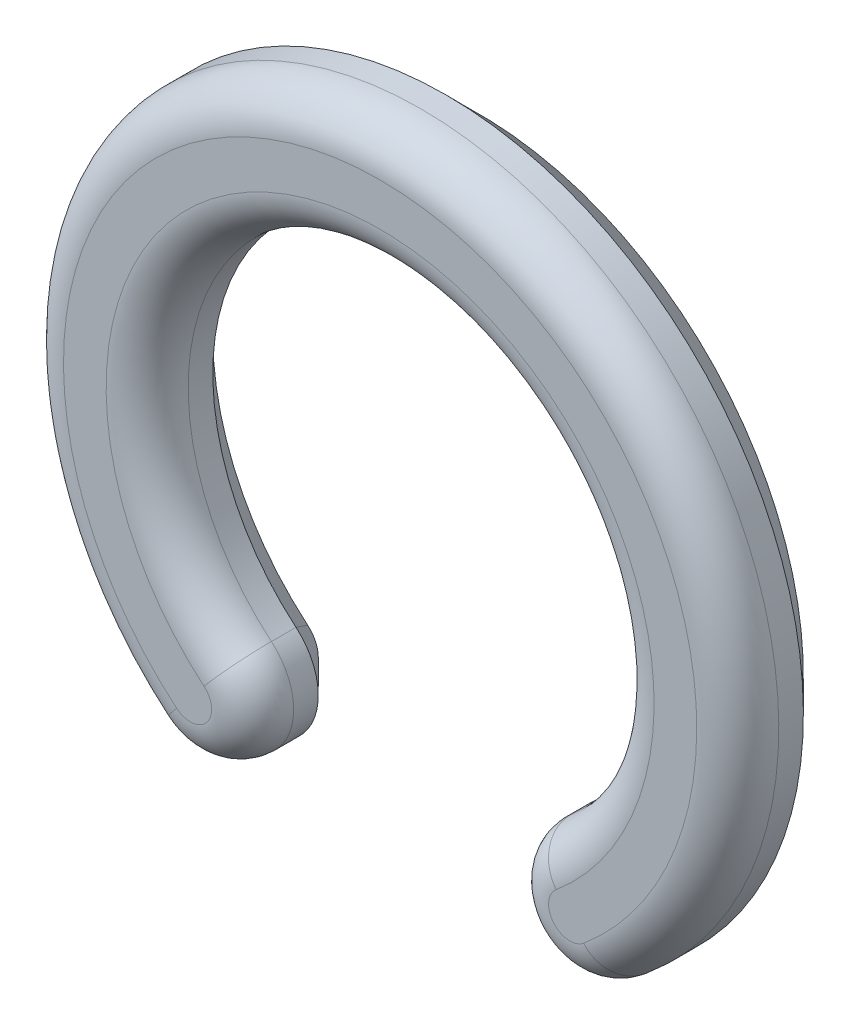
SolidWorks part; units mm, degrees
material "ABS"
ref_plane "Front Plane" through (0, 0, 0) normal (0, 0, 1) x (1, 0, 0)
ref_plane "Top Plane" through (0, 0, 0) normal (0, 1, 0) x (1, 0, 0)
ref_plane "Right Plane" through (0, 0, 0) normal (1, 0, 0) x (0, 0, -1)
sketch "Sketch1" plane through (0, 0, 0) normal (0, 0, 1) x (1, 0, 0)
  arc A0 (4.5638, -5.4389) -> (-4.5638, -5.4389) centre (0, 0) ccw
  arc A1 (7.0064, -8.3499) -> (-7.0064, -8.3499) centre (0, 0) ccw
  arc A2 (-7.0064, -8.3499) -> (-4.5638, -5.4389) centre (-5.7851, -6.8944) ccw
  arc A3 (4.5638, -5.4389) -> (7.0064, -8.3499) centre (5.7851, -6.8944) ccw
  point P1 (0, 0)
  dimension "D1" = 3.8
  dimension "D2" = 80
  dimension "D3" = 7.1
extrude "Boss-Extrude1" add sketch "Sketch1" along normal blind 3
chamfer "Chamfer1" distance 1 angle 45 4 edges at (0, 7.1, 0) (4.3296, -8.1157, 0) (-4.3296, -8.1157, 0) (0, 10.9, 0)
fillet "Fillet1" radius 1.25 4 edges at (-4.3296, -8.1157, 3) (0, 10.9, 3) (4.3296, -8.1157, 3) (0, 7.1, 3)
